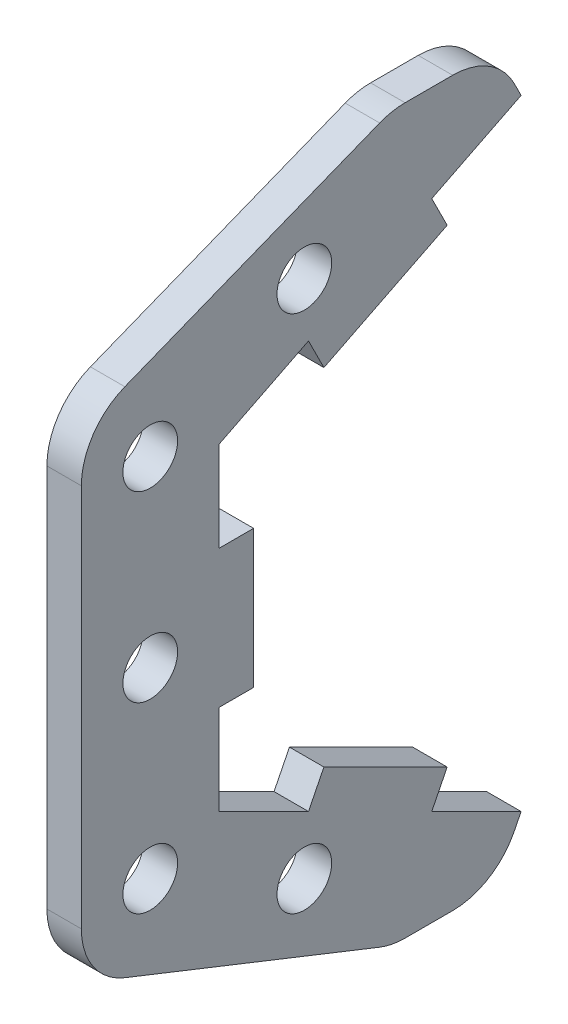
SolidWorks part; units mm, degrees
material "Plain Carbon Steel"
ref_plane "Front Plane" through (0, 0, 0) normal (0, 0, 1) x (1, 0, 0)
ref_plane "Top Plane" through (0, 0, 0) normal (0, 1, 0) x (1, 0, 0)
ref_plane "Right Plane" through (0, 0, 0) normal (1, 0, 0) x (0, 0, -1)
sketch "Sketch1" plane through (0, 0, 0) normal (1, 0, 0) x (0, 0, -1)
  line L0 (-160.655, 50.8) -> (93.345, 50.8)
  line L1 (93.345, 50.8) -> (93.345, -50.8)
  line L2 (93.345, -50.8) -> (-160.655, -50.8)
  line L3 (93.345, 0) -> (55.245, 50.8)
  line L4 (93.345, 0) -> (55.245, -50.8)
  circle A0 centre (0, 0) radius 38.1
  circle A1 centre (0, 0) radius 7.9375
  circle A2 centre (-38.1, 0) radius 7.9375
  circle A3 centre (-88.9, 0) radius 7.9375
  circle A4 centre (-88.9, 0) radius 39.751
  circle A5 centre (-38.1, 0) radius 25.4
  circle A6 centre (-160.655, 0) radius 11.1125
  circle A7 centre (-88.9, 0) radius 23.368
  circle A8 centre (-160.655, 0) radius 33.655
  circle A9 centre (-160.655, 0) radius 76.2
  circle A10 centre (-160.655, 0) radius 50.8
  dimension "D1" = 38.1
  dimension "D3" = 71.755
  dimension "D4" = 15.875
  dimension "D5" = 101.6
  dimension "D9" = 50.8
  dimension "D10" = 67.31
  dimension "D11" = 79.502
  dimension "D12" = 46.736
  dimension "D2" = 50.8
  dimension "D6" = 254
  dimension "D7" = 38.1
  dimension "D8" = 38.1
extrude "Boss-Extrude1" add sketch "Sketch1" along normal blind 12.7 contours A5 A0 A1 | A0 A5 | A10 A7 A9 A3 | A10 A7 A9 A4 | A7 A10 A4 | A7 A10 | A10 A4 A9 A7 | A9 A4 A5 A7 | A10 L2 A9 A4 | A4 A10 A8 | A8 A6 | A10 A4 A9 L0 | A9 A4 A5 A0 L2 L4 L3 L0 | A9 A3 A7 | A4 A5 | A0 A5 A4 A2 | A4 A8
hole_wizard "#8 Clearance Hole1" positions "Sketch3" profile "Sketch4" hole size "#8" standard "ANSI Inch" end condition through all
sketch "Sketch3" plane through (0, 0, 0) normal (-1, 0, 0) x (0, 0, 1)
  point P0 (-17.6911, 17.6911)
  point P3 (17.6911, 17.6911)
  point P6 (17.6911, -17.6911)
  point P9 (-17.6911, -17.6911)
sketch "Sketch4" plane through (0, 17.6911, -17.6911) normal (0, 1, 0) x (0, 0, 1)
  line L0 (0, 0) -> (0, 12.7)
  line L1 (0, 12.7) -> (2.2479, 12.7)
  line L2 (2.2479, 12.7) -> (2.2479, 0)
  line L5 (2.2479, 0) -> (0, 0)
  line L11 (0, -6.35) -> (0, 107.95) construction
  dimension "Thru Hole Dia." = 4.4958
  dimension "Thru Hole Depth" = 12.7
sketch "Sketch5" plane through (0, 0, 0) normal (-1, 0, 0) x (0, 0, 1)
  circle A0 centre (0, 0) radius 18.415
extrude "Cut-Extrude1" cut sketch "Sketch5" against normal through all
sketch "Sketch7" plane through (0, 0, 0) normal (-1, 0, 0) x (0, 0, 1)
  circle A0 centre (-55.245, 0) radius 9.525
  dimension "D1" = 38.1
extrude "Cut-Extrude2" cut sketch "Sketch7" against normal through all
sketch "Sketch8" plane through (12.7, 0, 0) normal (1, 0, 0) x (0, 0, -1)
  line L0 (-160.655, 50.8) -> (-211.455, 25.4)
  line L1 (-211.455, 25.4) -> (-211.455, -25.4)
  line L2 (-211.455, -25.4) -> (-160.655, -50.8)
  line L3 (-160.655, -50.8) -> (-233.2397, -50.8)
  line L4 (-233.2397, -50.8) -> (-233.2397, 50.8)
  line L5 (-233.2397, 50.8) -> (-160.655, 50.8)
  line L6 (-211.455, 0) -> (-160.655, 0) construction
  arc A0 (-160.655, 50.8) -> (-160.655, -50.8) centre (-160.655, 0) ccw construction
  dimension "D1" = 50.8
extrude "Cut-Extrude3" cut sketch "Sketch8" against normal through all
sketch "Sketch9" plane through (12.7, 0, 0) normal (1, 0, 0) x (0, 0, -1)
  line L0 (-160.655, 50.8) -> (-211.455, 25.4)
  line L1 (-211.455, 25.4) -> (-211.455, 0)
  line L2 (-211.455, 0) -> (-211.455, -25.4)
  line L3 (-211.455, -25.4) -> (-160.655, -50.8)
  line L4 (-160.655, -50.8) -> (-160.655, -40.64)
  line L5 (-160.655, -40.64) -> (-202.7493, 0)
  line L6 (-202.7493, 0) -> (-160.655, 40.64)
  line L7 (-160.655, 40.64) -> (-160.655, 50.8)
  line L8 (-160.655, -50.8) -> (-201.295, -30.48) construction
  line L9 (-201.295, 30.48) -> (-160.655, 50.8) construction
  arc A0 (-201.295, 30.48) -> (-201.295, -30.48) centre (-160.655, 0) ccw construction
extrude "Boss-Extrude2" add sketch "Sketch9" against normal blind 12.7
sketch "Sketch10" plane through (0, 0, 0) normal (-1, 0, 0) x (0, 0, 1)
  line L0 (-79.0575, -19.05) -> (-79.0575, 19.05)
  line L1 (-93.345, 0) -> (-55.245, -50.8) construction
  line L3 (-93.345, 0) -> (-55.245, 50.8) construction
  line L4 (-79.0575, 19.05) -> (-93.345, 0)
  line L5 (-93.345, 0) -> (-79.0575, -19.05)
extrude "Cut-Extrude4" cut sketch "Sketch10" against normal through all
sketch "Sketch11" plane through (0, 50.8, 0) normal (0, 1, 0) x (1, 0, 0)
  line L0 (0, -160.655) -> (0, 55.245) construction
  line L1 (0, 36.322) -> (12.7, 36.322)
  line L2 (0, 36.322) -> (0, -141.732)
  line L3 (0, -141.732) -> (12.7, -141.732)
  line L4 (12.7, 36.322) -> (12.7, -141.732)
  line L5 (12.7, -160.655) -> (12.7, 55.245) construction
  line L6 (12.7, -141.605) -> (0, -141.605) construction
  line L7 (0, 36.195) -> (12.7, 36.195) construction
  dimension "D1" = 0.127
  dimension "D2" = 0.127
extrude "Cut-Extrude5" cut sketch "Sketch11" against normal blind 3.175
mirror "Mirror1" about plane through (0, 0, 0) normal (0, 1, 0) of "Cut-Extrude5"
sketch "Sketch12" plane through (12.7, 0, 0) normal (1, 0, 0) x (0, 0, -1)
  line L16 (-162.154, 57.15) -> (-166.9165, 66.675)
  line L17 (-166.9165, 66.675) -> (-185.9665, 66.675)
  line L18 (-185.9665, 66.675) -> (-243.205, 43.9892)
  line L19 (-243.205, 43.9892) -> (-243.205, -43.9892)
  line L20 (-243.205, -43.9892) -> (-185.9665, -66.675)
  line L21 (-185.9665, -66.675) -> (-166.9165, -66.675)
  line L22 (-166.9165, -66.675) -> (-162.154, -57.15)
  line L23 (-243.205, 43.9892) -> (-217.805, 29.3245) construction
  line L24 (-217.805, -29.3245) -> (-243.205, -43.9892) construction
  line L32 (-162.154, -57.15) -> (-135.382, -57.15)
  line L33 (-135.382, -57.15) -> (-135.382, -53.975)
  line L34 (-135.382, -53.975) -> (29.972, -53.975)
  line L35 (29.972, -53.975) -> (29.972, -57.15)
  line L36 (29.972, -57.15) -> (58.42, -57.15)
  line L37 (58.42, -57.15) -> (85.4075, -21.1667)
  line L38 (85.4075, -21.1667) -> (85.4075, 21.1667)
  line L39 (85.4075, 21.1667) -> (58.42, 57.15)
  line L40 (58.42, 57.15) -> (29.972, 57.15)
  line L41 (29.972, 57.15) -> (29.972, 53.975)
  line L42 (29.972, 53.975) -> (-135.382, 53.975)
  line L43 (-135.382, 53.975) -> (-135.382, 57.15)
  line L44 (-135.382, 57.15) -> (-162.154, 57.15)
  line L45 (-162.154, 57.15) -> (-217.805, 29.3245)
  line L46 (-217.805, 29.3245) -> (-217.805, -29.3245)
  line L47 (-217.805, -29.3245) -> (-162.154, -57.15)
  line L48 (-162.154, -57.15) -> (-135.382, -57.15)
  line L49 (-135.382, -57.15) -> (-135.382, -53.975)
  line L50 (-135.382, -53.975) -> (29.972, -53.975)
  line L51 (29.972, -53.975) -> (29.972, -57.15)
  line L52 (29.972, -57.15) -> (58.42, -57.15)
  line L53 (58.42, -57.15) -> (85.4075, -21.1667)
  line L54 (85.4075, -21.1667) -> (85.4075, 21.1667)
  line L55 (85.4075, 21.1667) -> (58.42, 57.15)
  line L56 (58.42, 57.15) -> (29.972, 57.15)
  line L57 (29.972, 57.15) -> (29.972, 53.975)
  line L58 (29.972, 53.975) -> (-135.382, 53.975)
  line L59 (-135.382, 53.975) -> (-135.382, 57.15)
  line L60 (-135.382, 57.15) -> (-162.154, 57.15)
  line L61 (-162.154, 57.15) -> (-217.805, 29.3245)
  line L62 (-217.805, 29.3245) -> (-217.805, -29.3245)
  line L63 (-217.805, -29.3245) -> (-162.154, -57.15)
  circle A0 centre (-160.655, 0) radius 76.2
  dimension "D2" = 9.525
  dimension "D3" = 9.525
  dimension "D4" = 25.4
  dimension "D5" = 120
  dimension "D6" = 120
  dimension "D7" = 19.05
  dimension "D8" = 19.05
  dimension "D1" = 6.35
extrude "Boss-Extrude3" add sketch "Sketch12" against normal blind 6.35 separate body contours A0 L18 L19 L20 | L18 A0 L20 L21 L22 L63 L62 L61 L16 L17
sketch "Sketch13" plane through (12.7, 0, 0) normal (1, 0, 0) x (0, 0, -1)
  line L32 (-161.2546, -53.34) -> (-139.192, -53.34)
  line L33 (-139.192, -53.34) -> (-139.192, -50.165)
  line L34 (-139.192, -50.165) -> (33.782, -50.165)
  line L35 (33.782, -50.165) -> (33.782, -53.34)
  line L36 (33.782, -53.34) -> (56.515, -53.34)
  line L37 (56.515, -53.34) -> (81.5975, -19.8967)
  line L38 (81.5975, -19.8967) -> (81.5975, 19.8967)
  line L39 (81.5975, 19.8967) -> (56.515, 53.34)
  line L40 (56.515, 53.34) -> (33.782, 53.34)
  line L41 (33.782, 53.34) -> (33.782, 50.165)
  line L42 (33.782, 50.165) -> (-139.192, 50.165)
  line L43 (-139.192, 50.165) -> (-139.192, 53.34)
  line L44 (-139.192, 53.34) -> (-161.2546, 53.34)
  line L45 (-161.2546, 53.34) -> (-213.995, 26.9698)
  line L46 (-213.995, 26.9698) -> (-213.995, -26.9698)
  line L47 (-213.995, -26.9698) -> (-161.2546, -53.34)
  line L48 (-161.2546, -53.34) -> (-139.192, -53.34)
  line L49 (-139.192, -53.34) -> (-139.192, -50.165)
  line L50 (-139.192, -50.165) -> (33.782, -50.165)
  line L51 (33.782, -50.165) -> (33.782, -53.34)
  line L52 (33.782, -53.34) -> (56.515, -53.34)
  line L53 (56.515, -53.34) -> (81.5975, -19.8967)
  line L54 (81.5975, -19.8967) -> (81.5975, 19.8967)
  line L55 (81.5975, 19.8967) -> (56.515, 53.34)
  line L56 (56.515, 53.34) -> (33.782, 53.34)
  line L57 (33.782, 53.34) -> (33.782, 50.165)
  line L58 (33.782, 50.165) -> (-139.192, 50.165)
  line L59 (-139.192, 50.165) -> (-139.192, 53.34)
  line L60 (-139.192, 53.34) -> (-161.2546, 53.34)
  line L61 (-161.2546, 53.34) -> (-213.995, 26.9698)
  line L62 (-213.995, 26.9698) -> (-213.995, -26.9698)
  line L63 (-213.995, -26.9698) -> (-161.2546, -53.34)
  dimension "D1" = 2.54
extrude "Cut-Extrude6" cut sketch "Sketch13" against normal through all
hole_wizard "3/8 Clearance Hole1" positions "Sketch15" profile "Sketch14" hole size "3/8" standard "ANSI Inch"
sketch "Sketch15" plane through (12.7, 0, 0) normal (1, 0, 0) x (0, 0, -1)
  line L0 (-185.9665, -66.675) -> (-177.394, -49.53) construction
  line L1 (-217.805, -29.3245) -> (-162.154, -57.15) construction
  line L3 (-230.505, 49.0227) -> (-230.505, -49.0227) construction
  line L4 (-185.9665, 66.675) -> (-243.205, 43.9892) construction
  line L5 (-243.205, -43.9892) -> (-185.9665, -66.675) construction
  line L11 (-243.205, 0) -> (-230.505, 0) construction
  line L12 (-243.205, 43.9892) -> (-243.205, -43.9892) construction
  line L13 (-230.505, 0) -> (-217.805, 0) construction
  line L14 (-217.805, 29.3245) -> (-217.805, -29.3245) construction
  line L16 (-181.6803, -58.1025) -> (-230.505, -33.6901) construction
  line L18 (-185.9665, 66.675) -> (-177.394, 49.53) construction
  line L19 (-162.154, 57.15) -> (-217.805, 29.3245) construction
  line L23 (-230.505, 33.6901) -> (-181.6803, 58.1025) construction
  point P0 (-230.505, 0)
  point P2 (-230.505, 33.6901)
  point P4 (-202.1069, 47.8892)
  point P6 (-230.505, -33.6901)
  point P8 (-202.1069, -47.8892)
  dimension "D1" = 31.75
sketch "Sketch14" plane through (12.7, 0, 230.505) normal (0, 1, 0) x (0, 0, -1)
  line L0 (0, 0) -> (0, 15.7295)
  line L1 (0, 15.7295) -> (5.0419, 12.7)
  line L2 (5.0419, 12.7) -> (5.0419, 0)
  line L5 (5.0419, 0) -> (0, 0)
  line L10 (0, 15.7295) -> (-5.0419, 12.7) construction
  line L11 (0, -6.35) -> (0, 107.95) construction
  dimension "Hole Dia." = 10.0838
  dimension "Hole Depth" = 12.7
  dimension "Drill Angle" = 118
fillet "Fillet1" radius 12.7 6 edges at (9.525, 43.9892, 243.205) (9.525, -43.9892, 243.205) (9.525, -66.675, 166.9165) (9.525, -66.675, 185.9665) (9.525, 66.675, 166.9165) (9.525, 66.675, 185.9665)
sketch "Sketch16" plane through (12.7, 0, 0) normal (1, 0, 0) x (0, 0, -1)
  line L0 (-217.805, 29.3245) -> (-217.805, -29.3245) construction
  line L1 (-217.805, 12.7) -> (-211.455, 12.7)
  line L2 (-217.805, 12.7) -> (-217.805, -12.7)
  line L3 (-217.805, -12.7) -> (-211.455, -12.7)
  line L4 (-211.455, 12.7) -> (-211.455, -12.7)
  line L5 (-178.6203, -48.9169) -> (-175.7805, -43.2373)
  line L6 (-217.805, -29.3245) -> (-162.154, -57.15) construction
  line L7 (-175.7805, -43.2373) -> (-198.4989, -31.878)
  line L8 (-198.4989, -31.878) -> (-201.3387, -37.5576)
  line L9 (-201.3387, -37.5576) -> (-178.6203, -48.9169)
  line L10 (-201.3387, 37.5576) -> (-198.4989, 31.878)
  line L11 (-162.154, 57.15) -> (-217.805, 29.3245) construction
  line L12 (-198.4989, 31.878) -> (-175.7805, 43.2373)
  line L13 (-175.7805, 43.2373) -> (-178.6203, 48.9169)
  line L14 (-178.6203, 48.9169) -> (-201.3387, 37.5576)
  point P16 (-189.9795, 43.2373)
  point P19 (-189.9795, -43.2373)
  point P20 (-217.805, 0)
  dimension "D1" = 6.35
  dimension "D2" = 25.4
extrude "Boss-Extrude4" add sketch "Sketch16" against normal up to surface (6.35 mm away) up to face at (6.35, 0, 225.4631)
